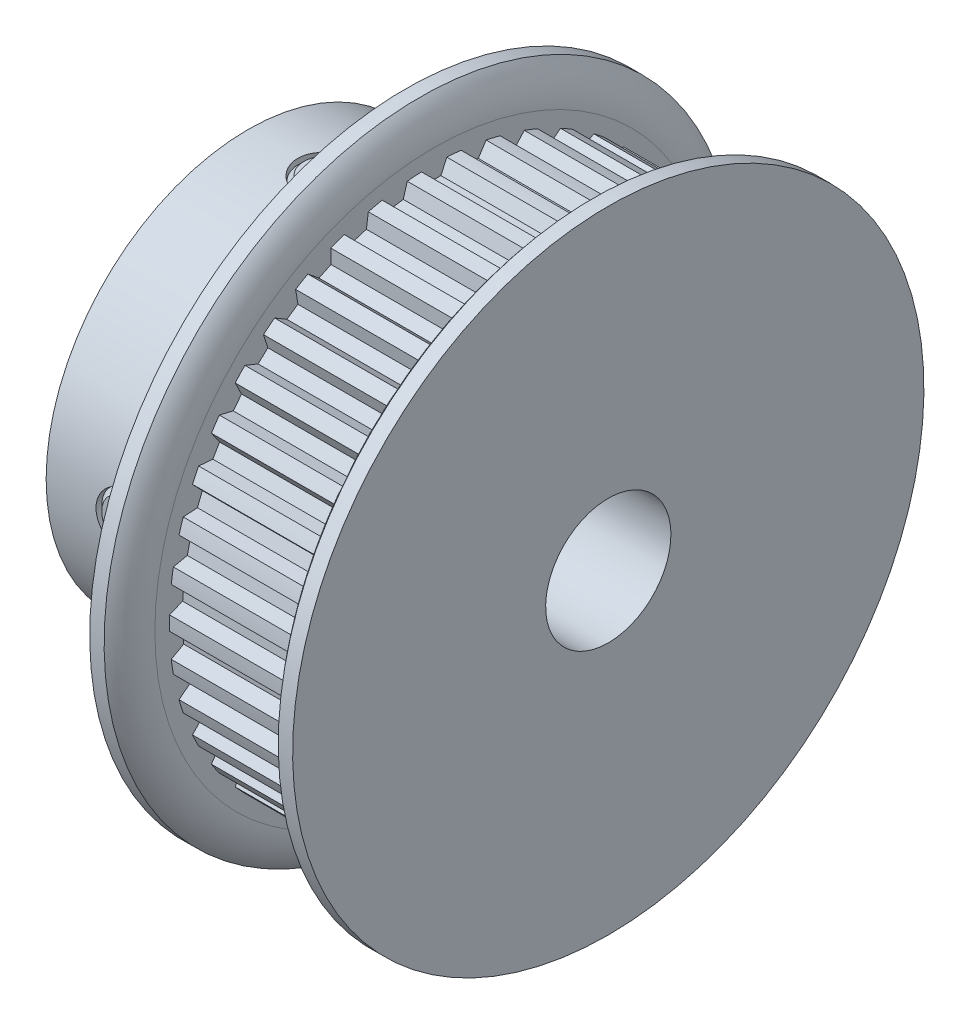
SolidWorks part; units mm, degrees
ref_plane "Front Plane" through (0, 0, 0) normal (0, 0, 1) x (1, 0, 0)
ref_plane "Top Plane" through (0, 0, 0) normal (0, 1, 0) x (1, 0, 0)
ref_plane "Right Plane" through (0, 0, 0) normal (1, 0, 0) x (0, 0, -1)
sketch "Sketch2" plane through (0, 0, 0) normal (1, 0, 0) x (0, 0, -1)
  line L3 (0, 0) -> (0, 12.7635) construction
  line L6 (0, -13.2715) -> (0, -13.589) construction
  line L7 (-0.5715, 13.2592) -> (-0.3383, 12.759)
  line L8 (0.5715, 13.2592) -> (0.3383, 12.759)
  line L9 (-0.5715, 13.2592) -> (-0.6441, 13.4148)
  line L10 (0.5715, 13.2592) -> (0.6441, 13.4148)
  line L12 (-0.3383, 12.759) -> (0.3383, 12.759)
  line L14 (0, 13.2715) -> (0, 13.589) construction
  line L15 (0, 0) -> (0, -1.143) construction
  circle A0 centre (0, 0) radius 13.589 construction
  circle A1 centre (0, 0) radius 12.7635 construction
  circle A2 centre (0, 0) radius 13.2715 construction
  arc A7 (0.6441, 13.4148) -> (-0.6441, 13.4148) centre (0, 0) ccw
  point P5 (0, 13.4303)
  dimension "D3" = 0.3175
  dimension "D1" = 50
sketch "Sketch1" plane through (0, 0, 0) normal (0, 0, 1) x (1, 0, 0)
  line L0 (-9.1313, 0) -> (9.1313, 0) construction
  line L1 (-9.1313, 3.175) -> (9.1313, 3.175)
  line L2 (-9.1313, 3.175) -> (-9.1313, 10.2362)
  line L3 (-1.1557, 16.002) -> (-0.4254, 16.002)
  line L4 (0.3048, 13.589) -> (0.3048, 14.1605)
  line L5 (0.3048, 14.732) -> (0.3048, 13.589) construction
  line L6 (0.3048, 13.589) -> (7.6708, 13.589)
  line L7 (7.6708, 13.589) -> (7.6708, 14.1605)
  line L8 (7.6708, 13.589) -> (9.1313, 13.589) construction
  line L9 (8.4011, 16.002) -> (9.1313, 16.002)
  line L10 (9.1313, 16.002) -> (9.1313, 3.175)
  line L11 (8.4011, 13.589) -> (8.4011, 16.002) construction
  line L12 (-5.1435, 10.2362) -> (-5.1435, 3.175) construction
  line L13 (-1.1557, 16.002) -> (-1.1557, 10.2362)
  line L14 (-1.1557, 10.2362) -> (-9.1313, 10.2362)
  arc A0 (7.6708, 14.1605) -> (8.4011, 16.002) centre (10.3578, 14.1605) cw
  arc A1 (0.3048, 14.1605) -> (-0.4254, 16.002) centre (-2.3822, 14.1605) ccw
  dimension "Bore Size" = 6.35
  dimension "Overall Width" = 18.2626
  dimension "Inside Width" = 7.366
  dimension "OD" = 32.004
  dimension "D2" = 27.178
  dimension "D3" = 1.143
  dimension "D4" = 0.5715
  dimension "Outside Width" = 10.287
revolve "Revolve1" add sketch "Sketch1" angle 360 mid plane about L0
sketch "Sketch4" plane through (0.3048, 0, 0) normal (1, 0, 0) x (0, 0, -1)
  circle A0 centre (0, 0) radius 13.4303
  circle A2 centre (0, 0) radius 13.589
  circle A3 centre (0, 0) radius 13.589 construction
extrude "Cut-Extrude2" cut sketch "Sketch4" along normal up to surface (7.366 mm away) up to face at (7.6708, -13.589, 0)
sketch "Sketch3" plane through (0.3048, 0, 0) normal (1, 0, 0) x (0, 0, -1)
  line L2 (-0.5715, 13.2592) -> (-0.3383, 12.759) construction
  line L3 (-0.3383, 12.759) -> (0.3383, 12.759) construction
  line L4 (0.5715, 13.2592) -> (0.3383, 12.759) construction
  line L5 (-0.6441, 13.4148) -> (-0.3383, 12.759)
  line L6 (-0.3383, 12.759) -> (0.3383, 12.759)
  line L7 (0.6441, 13.4148) -> (0.3383, 12.759)
  arc A1 (0.6441, 13.4148) -> (-0.6441, 13.4148) centre (0, 0) ccw construction
  arc A2 (0.6441, 13.4148) -> (-0.6441, 13.4148) centre (0, 0) ccw
extrude "Cut-Extrude1" cut sketch "Sketch3" along normal up to surface (7.366 mm away) up to face at (7.6708, -14.1605, 0)
pattern_circular "CirPattern1" count 42 over 360 about axis through (0, 0, 0) along (1, 0, 0) of "Cut-Extrude1"
sketch "Sketch5" plane through (0, 0, 0) normal (0, 0, 1) x (1, 0, 0)
  line L1 (7.6708, 14.1605) -> (7.6708, -14.1605) construction
  point P0 (7.6708, 0)
sketch "Sketch6" plane through (0, 0, 0) normal (0, 1, 0) x (1, 0, 0)
  line L0 (-9.1313, 0) -> (-6.604, 0) construction
  line L1 (-9.1313, 16.002) -> (-9.1313, -16.002) construction
  line L2 (-1.1557, 0) -> (-3.683, 0) construction
  line L4 (-1.1557, 16.002) -> (-1.1557, -16.002) construction
  circle A0 centre (-5.1435, 0) radius 1.4605
  dimension "D1" = 2.921
extrude "Cut-Extrude3" cut sketch "Sketch6" along normal through all
sketch "Sketch7" plane through (0, 0, 0) normal (0, 0, 1) x (1, 0, 0)
  line L0 (-6.3119, 10.2362) -> (-5.1435, 10.2362)
  line L1 (-6.5659, 9.9822) -> (-6.5659, 3.81)
  line L2 (-6.5659, 3.81) -> (-6.3119, 3.556)
  line L3 (-6.3119, 3.556) -> (-5.1435, 3.556)
  line L4 (-5.1435, 3.556) -> (-5.1435, 10.2362) construction
  line L5 (-1.1557, 10.2362) -> (-9.1313, 10.2362) construction
  line L6 (-6.5659, 9.9822) -> (-6.3119, 10.2362)
  line L8 (-5.1435, 10.2362) -> (-5.1435, 3.556)
  point P0 (-6.5659, 10.2362)
  point P4 (-6.5659, 3.556)
  dimension "D1" = 2.8448
  dimension "D2" = 0.381
revolve "Revolve2" add sketch "Sketch7" angle 360 mid plane about L4
sketch "Sketch8" plane through (0, 10.2362, 0) normal (0, 1, 0) x (1, 0, 0)
  line L1 (-5.1435, 0.8212) -> (-5.8547, 0.4106)
  line L2 (-5.8547, 0.4106) -> (-5.8547, -0.4106)
  line L3 (-5.8547, -0.4106) -> (-5.1435, -0.8212)
  line L4 (-5.1435, -0.8212) -> (-4.4323, -0.4106)
  line L5 (-4.4323, -0.4106) -> (-4.4323, 0.4106)
  line L6 (-4.4323, 0.4106) -> (-5.1435, 0.8212)
  circle A0 centre (-5.1435, 0) radius 0.7112 construction
  dimension "D1" = 1.4224
extrude "Cut-Extrude4" cut sketch "Sketch8" against normal blind 1.016
pattern_circular "CirPattern2" count 2 over 90 about axis through (-9.1313, 0, 0) along (-1, 0, 0) of "Cut-Extrude3"
pattern_circular "CirPattern3" count 2 over 90 about axis through (0, 0, 0) along (1, 0, 0) of bodies 107
sketch "Sketch9" plane through (-9.1313, 0, 0) normal (-1, 0, 0) x (0, 0, 1)
  circle A0 centre (0, 0) radius 6.35
  dimension "D1" = 12.7
equation "\"D3@Sketch2\" = (\"hs@Sketch2\"-\"ht@Sketch2\")/2"
equation "\"D2@Sketch1\" = \"PD@Sketch2\""
equation "\"D3@Sketch1\" = \"hs@Sketch2\""
equation "\"D4@Sketch1\" = \"D3@Sketch1\"/2"
